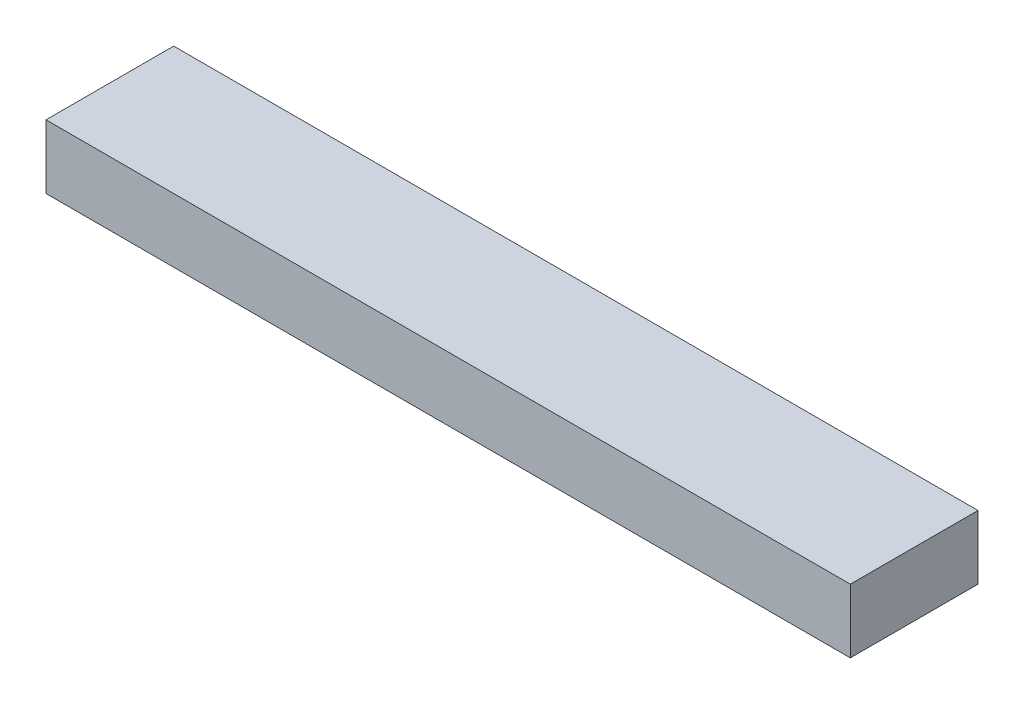
SolidWorks part; units mm, degrees
ref_plane "Front Plane" through (0, 0, 0) normal (0, 0, 1) x (1, 0, 0)
ref_plane "Top Plane" through (0, 0, 0) normal (0, 1, 0) x (1, 0, 0)
ref_plane "Right Plane" through (0, 0, 0) normal (1, 0, 0) x (0, 0, -1)
sketch "Sketch1" plane through (0, 0, 0) normal (1, 0, 0) x (0, 0, -1)
  line L1 (0, 0) -> (50.8, 0)
  line L2 (0, 0) -> (0, 25.4)
  line L3 (0, 25.4) -> (50.8, 25.4)
  line L4 (50.8, 0) -> (50.8, 25.4)
  dimension "D1" = 50.8
  dimension "D2" = 25.4
extrude "Boss-Extrude1" add sketch "Sketch1" along normal blind 320
